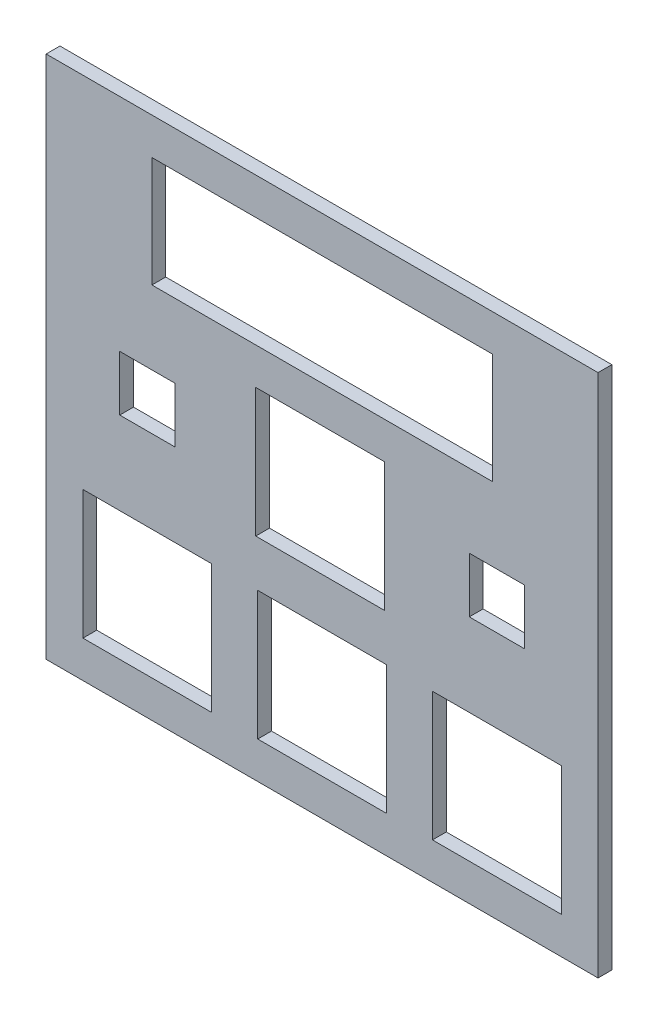
SolidWorks part; units mm, degrees
ref_plane "Plan de face" through (0, 0, 0) normal (0, 0, 1) x (1, 0, 0)
ref_plane "Plan de dessus" through (0, 0, 0) normal (0, 1, 0) x (1, 0, 0)
ref_plane "Plan de droite" through (0, 0, 0) normal (1, 0, 0) x (0, 0, -1)
sketch "Sketch1" plane through (0, 0, 0) normal (0, 0, 1) x (1, 0, 0)
  line L1 (-29.7, 15.8415) -> (30.3, 15.8415)
  line L2 (-29.7, 15.8415) -> (-29.7, -41.1585)
  line L3 (-29.7, -41.1585) -> (30.3, -41.1585)
  line L4 (30.3, 15.8415) -> (30.3, -41.1585)
  line L5 (-25.7, -37.1585) -> (-11.7, -37.1585)
  line L6 (-25.7, -37.1585) -> (-25.7, -23.1585)
  line L7 (-25.7, -23.1585) -> (-11.7, -23.1585)
  line L8 (-11.7, -37.1585) -> (-11.7, -23.1585)
  line L9 (-6.7, -37.1585) -> (7.3, -37.1585)
  line L10 (-6.7, -37.1585) -> (-6.7, -23.1585)
  line L11 (-6.7, -23.1585) -> (7.3, -23.1585)
  line L12 (7.3, -37.1585) -> (7.3, -23.1585)
  line L13 (12.3, -23.1585) -> (26.3, -23.1585)
  line L14 (12.3, -23.1585) -> (12.3, -37.1585)
  line L15 (12.3, -37.1585) -> (26.3, -37.1585)
  line L16 (26.3, -23.1585) -> (26.3, -37.1585)
  line L17 (-6.9147, -18.1585) -> (7.0853, -18.1585)
  line L18 (-6.9147, -18.1585) -> (-6.9147, -4.1585)
  line L19 (-6.9147, -4.1585) -> (7.0853, -4.1585)
  line L20 (7.0853, -18.1585) -> (7.0853, -4.1585)
  line L21 (-18.2, 11.8415) -> (18.8, 11.8415)
  line L22 (-18.2, 11.8415) -> (-18.2, -0.1585)
  line L23 (-18.2, -0.1585) -> (18.8, -0.1585)
  line L24 (18.8, 11.8415) -> (18.8, -0.1585)
  line L25 (-21.7, -8.1585) -> (-15.7, -8.1585)
  line L26 (-21.7, -8.1585) -> (-21.7, -14.1585)
  line L27 (-21.7, -14.1585) -> (-15.7, -14.1585)
  line L28 (-15.7, -8.1585) -> (-15.7, -14.1585)
  line L29 (16.3, -14.1585) -> (22.3, -14.1585)
  line L30 (16.3, -14.1585) -> (16.3, -8.1585)
  line L31 (16.3, -8.1585) -> (22.3, -8.1585)
  line L32 (22.3, -14.1585) -> (22.3, -8.1585)
  point P28 (-6.9147, -11.1585)
  point P29 (-18.7, -14.1585)
  dimension "D1" = 60
  dimension "D2" = 57
  dimension "D3" = 14
  dimension "D4" = 14
  dimension "D5" = 4
  dimension "D6" = 4
  dimension "D7" = 14
  dimension "D8" = 14
  dimension "D9" = 5
  dimension "D10" = 5
  dimension "D11" = 4
  dimension "D12" = 14
  dimension "D13" = 5
  dimension "D14" = 37
  dimension "D15" = 12
  dimension "D16" = 11.5
  dimension "D17" = 4
  dimension "D18" = 0
  dimension "D19" = 4
  dimension "D20" = 6
  dimension "D21" = 6
  dimension "D22" = 3
  dimension "D23" = 7
  dimension "D24" = 0
  dimension "D25" = 0
  dimension "D26" = 6
  dimension "D27" = 8
extrude "Boss-Extrude1" add sketch "Sketch1" along normal blind 1.5
